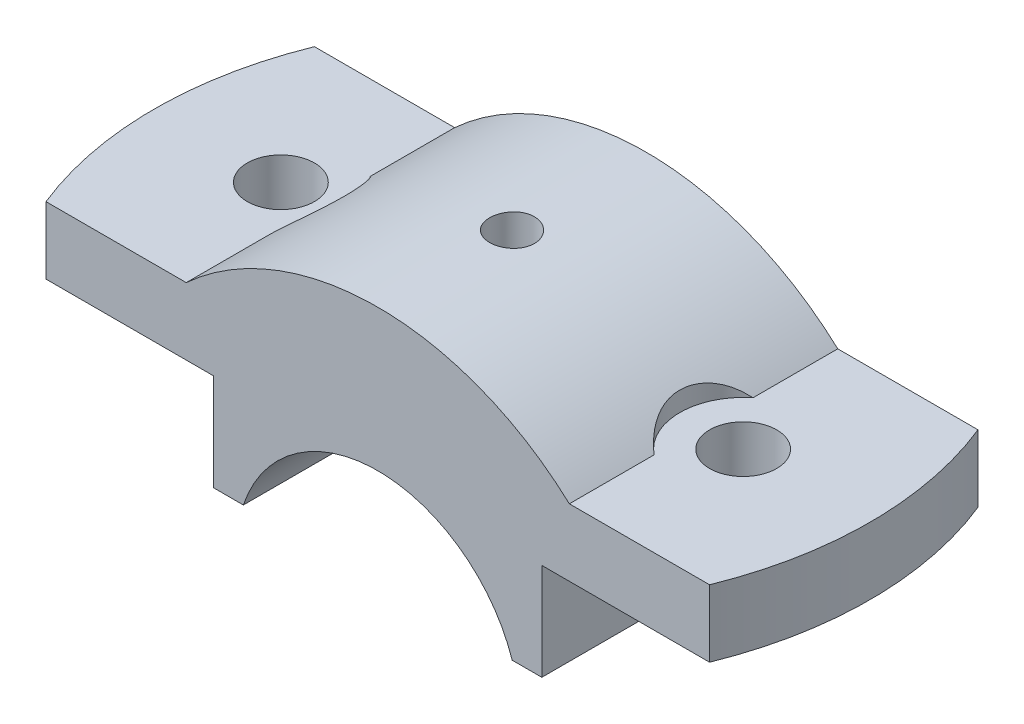
SolidWorks part; units mm, degrees
ref_plane "Front Plane" through (0, 0, 0) normal (0, 0, 1) x (1, 0, 0)
ref_plane "Top Plane" through (0, 0, 0) normal (0, 1, 0) x (1, 0, 0)
ref_plane "Right Plane" through (0, 0, 0) normal (1, 0, 0) x (0, 0, -1)
sketch "Sketch1" plane through (0, 0, 0) normal (0, 0, 1) x (1, 0, 0)
  line L0 (0, 0) -> (0, 63.2139) construction
  line L1 (18.0278, 6) -> (22, 6)
  line L2 (22, 6) -> (22, 19)
  line L3 (22, 19) -> (50, 19)
  line L4 (50, 19) -> (50, 28)
  line L5 (50, 28) -> (25.6905, 28)
  line L6 (-18.0278, 6) -> (-22, 6)
  line L7 (-22, 6) -> (-22, 19)
  line L8 (-22, 19) -> (-50, 19)
  line L9 (-50, 19) -> (-50, 28)
  line L10 (-50, 28) -> (-25.6905, 28)
  arc A0 (25.6905, 28) -> (-25.6905, 28) centre (0, 0) ccw
  arc A1 (18.0278, 6) -> (-18.0278, 6) centre (0, 0) ccw
  dimension "D1" = 19
  dimension "D2" = 38
  dimension "D3" = 6
  dimension "D4" = 13
  dimension "D5" = 9
  dimension "D6" = 44
  dimension "D7" = 50
extrude "Boss-Extrude1" add sketch "Sketch1" along normal mid plane 36
sketch "Sketch2" plane through (0, 28, 0) normal (0, 1, 0) x (1, 0, 0)
  line L0 (-25.6905, 18) -> (-50, 18) construction
  line L1 (-50, -18) -> (-50, 18) construction
  line L2 (-25.6905, -18) -> (-50, -18) construction
  line L3 (-44.4972, 18) -> (-50, 18)
  line L4 (-50, -18) -> (-50, 18)
  line L5 (-44.4972, -18) -> (-50, -18)
  arc A0 (-44.4972, 18) -> (-44.4972, -18) centre (0, 0) ccw
  dimension "D1" = 48
extrude "Cut-Extrude1" cut sketch "Sketch2" against normal blind 9
hole_wizard "Ø16.0mm Dowel Hole21" positions "Sketch74" profile "Sketch73" hole size "Ø16.0" standard "ANSI Metric"
sketch "Sketch74" plane through (0, 28, 0) normal (0, 1, 0) x (1, 0, 0)
  point P0 (-31, 0)
  dimension "D1" = 31
sketch "Sketch73" plane through (-31, 28, 0) normal (1, 0, 0) x (0, 0, 1)
  line L0 (0, 0) -> (0, 11.7039)
  line L1 (0, 11.7039) -> (4.5, 9)
  line L2 (4.5, 9) -> (4.5, 0)
  line L5 (4.5, 0) -> (0, 0)
  line L10 (0, 11.7039) -> (-4.5, 9) construction
  line L11 (0, -6.35) -> (0, 107.95) construction
  dimension "Hole Dia." = 9
  dimension "Hole Depth" = 9
  dimension "Drill Angle" = 118
sketch3d "3DSketch2"
  line L0 (-25.6905, 28, 18) -> (-25.6905, 28, -18) construction
  line L1 (-25.6905, 28, 6.6377) -> (-25.6905, 28, -6.6377)
  line L2 (-31, 19, 0) -> (-31, 28, 0) construction
  arc A0 (-25.6905, 28, 6.6377) -> (-25.6905, 28, -6.6377) centre (-31, 28, 0) ccw
  point P4 (-31, 36.5, 0)
  dimension "D1" = 8.5
extrude "Cut-Extrude2" cut sketch "3DSketch2" along direction (0, 1, 0) on the side of the normal through all
mirror "Mirror2" about plane through (0, 0, 0) normal (1, 0, 0) of "Ø16.0mm Dowel Hole21", "Cut-Extrude2"
hole_wizard "CBORE for M6 Hex Head Machine Screw4" positions "3DSketch13" profile "Sketch85" counterbore size "M6" standard "ANSI Metric" end condition through all
sketch3d "3DSketch13"
  point P0 (0, 38, 0)
  dimension "D1" = 0
  dimension "D2" = 0
sketch "Sketch85" plane through (0, 38, 0) normal (1, 0, 0) x (0, 0, 1)
  line L0 (0, 0) -> (0, 32)
  line L1 (0, 32) -> (2.5, 32)
  line L2 (2.5, 13.495) -> (2.5, 32)
  line L3 (2.5, 13.495) -> (2.995, 13)
  line L4 (2.995, 13) -> (3, 13)
  line L5 (3, 13) -> (3, 0)
  line L7 (0, 0) -> (3, 0)
  line L9 (-2.5, 13.495) -> (-2.995, 13) construction
  line L11 (0, -6.35) -> (0, 107.95) construction
  dimension "Thru Hole Dia." = 5
  dimension "Thru Hole Depth" = 32
  dimension "C'Bore Dia." = 6
  dimension "C'Bore Depth" = 13
  dimension "Mid C'Sink Dia." = 5.99
  dimension "Mid C'Sink Angle" = 90
mirror "Mirror4" about plane through (0, 0, 0) normal (1, 0, 0) of "Cut-Extrude1"
